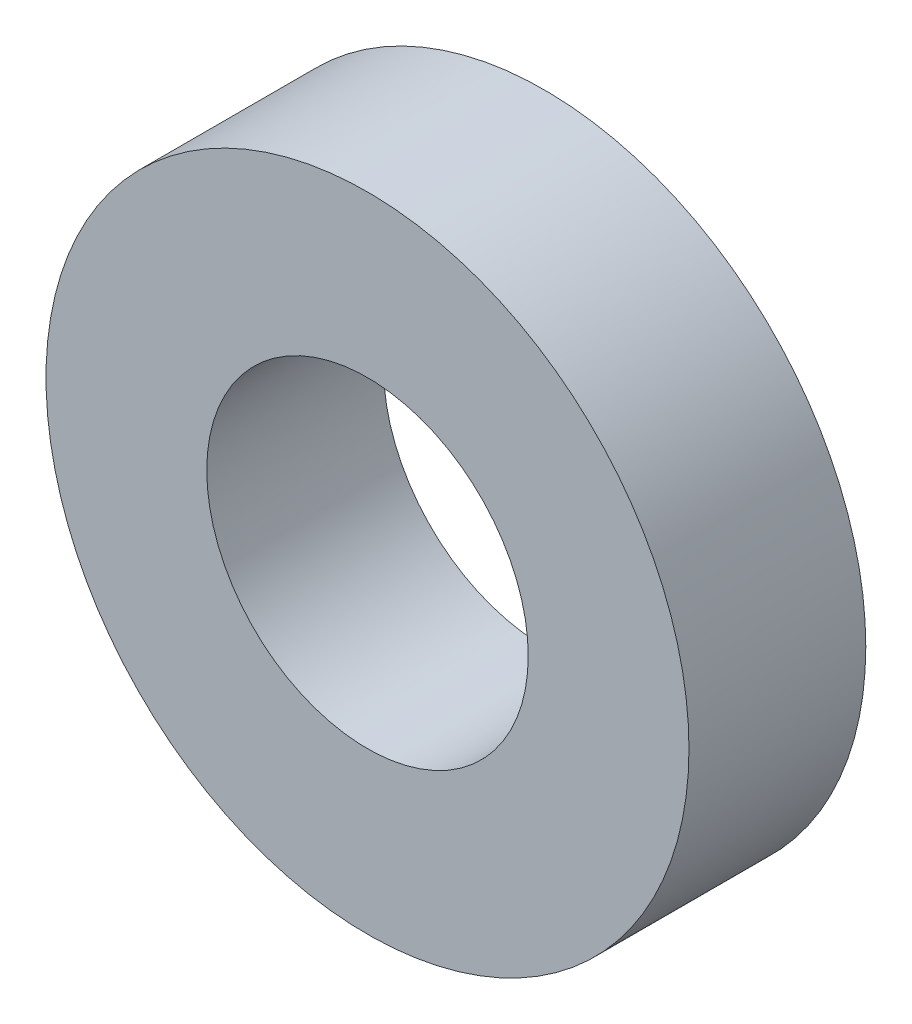
SolidWorks part; units mm, degrees
ref_plane "Front Plane" through (0, 0, 0) normal (0, 0, 1) x (1, 0, 0)
ref_plane "Top Plane" through (0, 0, 0) normal (0, 1, 0) x (1, 0, 0)
ref_plane "Right Plane" through (0, 0, 0) normal (1, 0, 0) x (0, 0, -1)
sketch "Sketch1" plane through (0, 0, 0) normal (0, 0, 1) x (1, 0, 0)
  circle A0 centre (0, 0) radius 10
  circle A1 centre (0, 0) radius 20
  dimension "D1" = 40
  dimension "D2" = 20
extrude "Boss-Extrude1" add sketch "Sketch1" along normal blind 11
